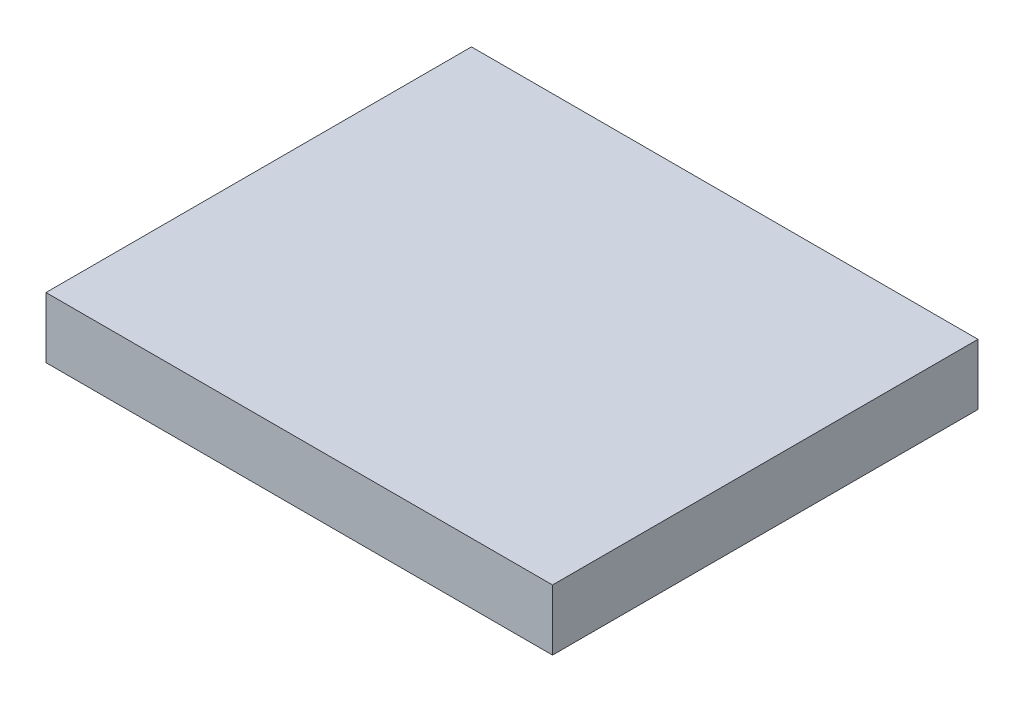
SolidWorks part; units mm, degrees
ref_plane "Front Plane" through (0, 0, 0) normal (0, 0, 1) x (1, 0, 0)
ref_plane "Top Plane" through (0, 0, 0) normal (0, 1, 0) x (1, 0, 0)
ref_plane "Right Plane" through (0, 0, 0) normal (1, 0, 0) x (0, 0, -1)
sketch "Sketch1" plane through (0, 0, 0) normal (0, 1, 0) x (1, 0, 0)
  line L1 (-19.8437, -16.6687) -> (19.8438, -16.6687)
  line L2 (-19.8437, -16.6687) -> (-19.8437, 16.6688)
  line L3 (-19.8437, 16.6688) -> (19.8438, 16.6688)
  line L4 (19.8438, -16.6687) -> (19.8438, 16.6688)
  line L5 (-19.8437, -16.6687) -> (19.8438, 16.6688) construction
  line L6 (-19.8437, 16.6688) -> (19.8438, -16.6687) construction
  point P0 (0, 0)
  dimension "D1" = 33.3375
  dimension "D2" = 39.6875
extrude "Boss-Extrude1" add sketch "Sketch1" along normal blind 4.7625
